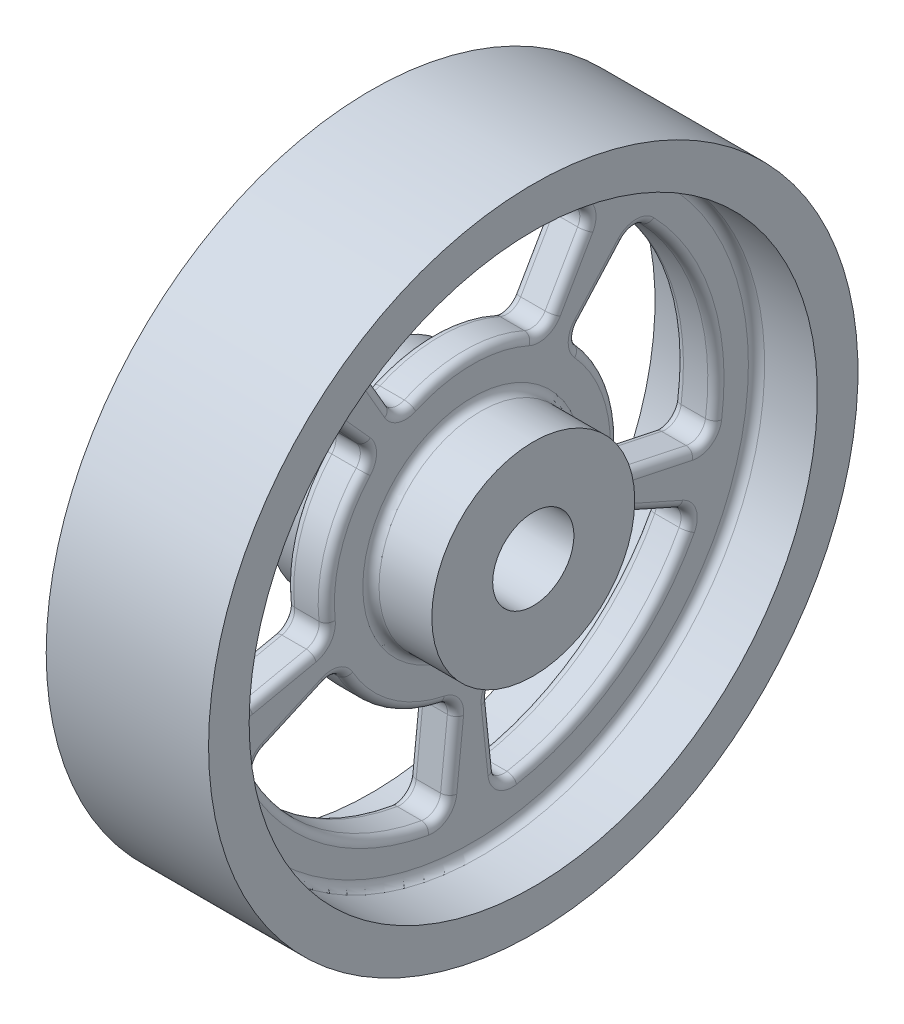
SolidWorks part; units mm, degrees
ref_plane "Front Plane" through (0, 0, 0) normal (0, 0, 1) x (1, 0, 0)
ref_plane "Top Plane" through (0, 0, 0) normal (0, 1, 0) x (1, 0, 0)
ref_plane "Right Plane" through (0, 0, 0) normal (1, 0, 0) x (0, 0, -1)
sketch "Sketch1" plane through (0, 0, 0) normal (0, 1, 0) x (1, 0, 0)
  line L0 (2.5, 35) -> (10, 35)
  line L1 (-10, 40) -> (10, 40)
  line L2 (-10, 40) -> (-10, 35)
  line L3 (-10, 35) -> (-2.5, 35)
  line L4 (10, 40) -> (10, 35)
  line L6 (-2.5, 12.5) -> (-2.5, 35)
  line L8 (2.5, 12.5) -> (2.5, 35)
  line L9 (-10, 12.5) -> (-2.5, 12.5)
  line L10 (-10, 12.5) -> (-10, 5)
  line L11 (-10, 5) -> (10, 5)
  line L12 (10, 12.5) -> (10, 5)
  line L13 (2.5, 12.5) -> (10, 12.5)
  line L14 (0, 0) -> (0, 99.5392) construction
  line L15 (0, 0) -> (137.8832, 0) construction
  line L18 (-10, 35) -> (-10, 12.5) construction
  line L19 (10, 35) -> (10, 12.5) construction
  point P15 (-83.9364, 132.5052)
  dimension "D1" = 20
  dimension "D2" = 5
  dimension "D3" = 10
  dimension "D4" = 25
  dimension "D5" = 80
  dimension "D6" = 5
revolve "Revolve1" add sketch "Sketch1" angle 360 about L15
sketch "Sketch4" plane through (2.5, 0, 0) normal (1, 0, 0) x (0, 0, -1)
  line L2 (0, 0) -> (0, 62.1861) construction
  line L3 (-15, 25.9808) -> (-9, 15.5885)
  line L4 (9, 15.5885) -> (15, 25.9808)
  arc A2 (-9, 15.5885) -> (9, 15.5885) centre (0, 0) cw
  arc A3 (-15, 25.9808) -> (15, 25.9808) centre (0, 0) cw
  point P6 (0, 0)
  point P8 (0, 0)
  point P9 (0, 0)
  point P10 (0, 0)
  dimension "D1" = 18
  dimension "D2" = 30
  dimension "D3" = 60
extrude "Cut-Extrude2" cut sketch "Sketch4" against normal through all contours L4 A3 L3 A2
fillet "Fillet2" radius 2 4 edges at (0, 15.5885, -9) (0, 15.5885, 9) (0, 25.9808, -15) (0, 25.9808, 15)
pattern_circular "CirPattern1" count 5 over 360 about axis through (0, 0, 0) along (1, 0, 0) of "Cut-Extrude2", "Fillet2"
fillet "Fillet3" radius 1 84 edges at (2.5, 0, 12.5) (2.5, 0, 35) (2.5, 25.7731, -14.1443) (2.5, 30, 0) (2.5, 25.7731, 14.1443) (2.5, 20.7102, 11.9571) (2.5, 16.3302, 8.8315) (2.5, 18, 0) (2.5, 16.3302, -8.8315) (2.5, 20.7102, -11.9571) (2.5, -5.4877, -28.8825) (2.5, 9.2705, -28.5317) (2.5, 21.4164, -20.1409) (2.5, 17.7717, -16.0017) (2.5, 13.4456, -12.8018) (2.5, 5.5623, -17.119) (2.5, -3.353, -18.26) (2.5, -4.972, -23.3915) (2.5, -29.1647, -3.7061) (2.5, -24.2705, -17.6336) (2.5, -12.5371, -26.592) (2.5, -9.7267, -21.8466) (2.5, -8.0203, -16.7435) (2.5, -14.5623, -10.5801) (2.5, -18.4024, -2.4538) (2.5, -23.7831, -2.4997) (2.5, -12.5371, 26.592) (2.5, -24.2705, 17.6336) (2.5, -29.1647, 3.7061) (2.5, -23.7831, 2.4997) (2.5, -18.4024, 2.4538) (2.5, -14.5623, 10.5801) (2.5, -8.0203, 16.7435) (2.5, -9.7267, 21.8466) (2.5, 21.4164, 20.1409) (2.5, 9.2705, 28.5317) (2.5, -5.4877, 28.8825) (2.5, -4.972, 23.3915) (2.5, -3.353, 18.26) (2.5, 5.5623, 17.119) (2.5, 13.4456, 12.8018) (2.5, 17.7717, 16.0017) (-2.5, 0, 35) (-2.5, 0, 12.5) (-2.5, 25.7731, -14.1443) (-2.5, 20.7102, -11.9571) (-2.5, 16.3302, -8.8315) (-2.5, 18, 0) (-2.5, 16.3302, 8.8315) (-2.5, 20.7102, 11.9571) (-2.5, 25.7731, 14.1443) (-2.5, 30, 0) (-2.5, -5.4877, -28.8825) (-2.5, -4.972, -23.3915) (-2.5, -3.353, -18.26) (-2.5, 5.5623, -17.119) (-2.5, 13.4456, -12.8018) (-2.5, 17.7717, -16.0017) (-2.5, 21.4164, -20.1409) (-2.5, 9.2705, -28.5317) (-2.5, -29.1647, -3.7061) (-2.5, -23.7831, -2.4997) (-2.5, -18.4024, -2.4538) (-2.5, -14.5623, -10.5801) (-2.5, -8.0203, -16.7435) (-2.5, -9.7267, -21.8466) (-2.5, -12.5371, -26.592) (-2.5, -24.2705, -17.6336) (-2.5, -12.5371, 26.592) (-2.5, -9.7267, 21.8466) (-2.5, -8.0203, 16.7435) (-2.5, -14.5623, 10.5801) (-2.5, -18.4024, 2.4538) (-2.5, -23.7831, 2.4997) (-2.5, -29.1647, 3.7061) (-2.5, -24.2705, 17.6336) (-2.5, 21.4164, 20.1409) (-2.5, 17.7717, 16.0017) (-2.5, 13.4456, 12.8018) (-2.5, 5.5623, 17.119) (-2.5, -3.353, 18.26) (-2.5, -4.972, 23.3915) (-2.5, -5.4877, 28.8825) (-2.5, 9.2705, 28.5317)
